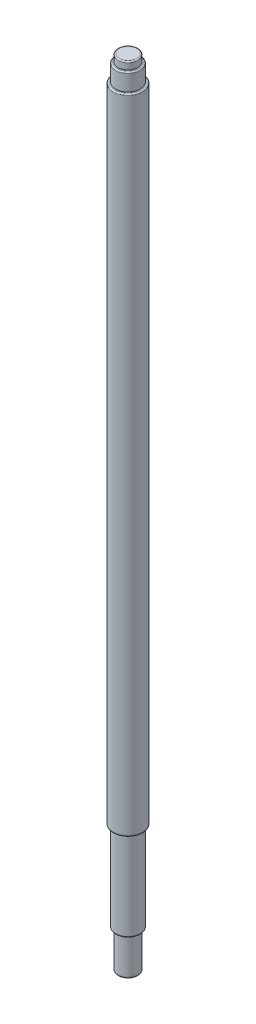
SolidWorks part; units mm, degrees
ref_plane "前视基准面" through (0, 0, 0) normal (0, 0, 1) x (1, 0, 0)
ref_plane "上视基准面" through (0, 0, 0) normal (0, 1, 0) x (1, 0, 0)
ref_plane "右视基准面" through (0, 0, 0) normal (1, 0, 0) x (0, 0, -1)
other "Configuration Table"
sketch "草图1" plane through (0, 0, 0) normal (0, 1, 0) x (1, 0, 0)
  circle A0 centre (0, 0) radius 4
  dimension "D1" = 8
extrude "凸台-拉伸1" add sketch "草图1" along normal blind 15
sketch "草图2" plane through (0, 15, 0) normal (0, 1, 0) x (1, 0, 0)
  circle A0 centre (0, 0) radius 5
extrude "凸台-拉伸2" add sketch "草图2" along normal blind 36
sketch "草图3" plane through (0, 51, 0) normal (0, 1, 0) x (1, 0, 0)
  circle A0 centre (0, 0) radius 6
extrude "凸台-拉伸3" add sketch "草图3" along normal blind 260
sketch "草图4" plane through (0, 311, 0) normal (0, 1, 0) x (1, 0, 0)
  circle A0 centre (0, 0) radius 5
extrude "凸台-拉伸4" add sketch "草图4" along normal blind 7
sketch "草图5" plane through (0, 318, 0) normal (0, 1, 0) x (1, 0, 0)
  circle A0 centre (0, 0) radius 4
extrude "凸台-拉伸5" add sketch "草图5" along normal blind 3
fillet "圆角1" radius 0.5 1 edges at (0, 321, 4)
fillet "圆角2" radius 0.5 1 edges at (0, 318, 5)
fillet "圆角3" radius 0.5 1 edges at (0, 311, 6)
fillet "圆角4" radius 0.5 1 edges at (0, 51, 6)
fillet "圆角5" radius 0.5 1 edges at (0, 15, 5)
fillet "圆角6" radius 0.5 1 edges at (0, 0, 4)
